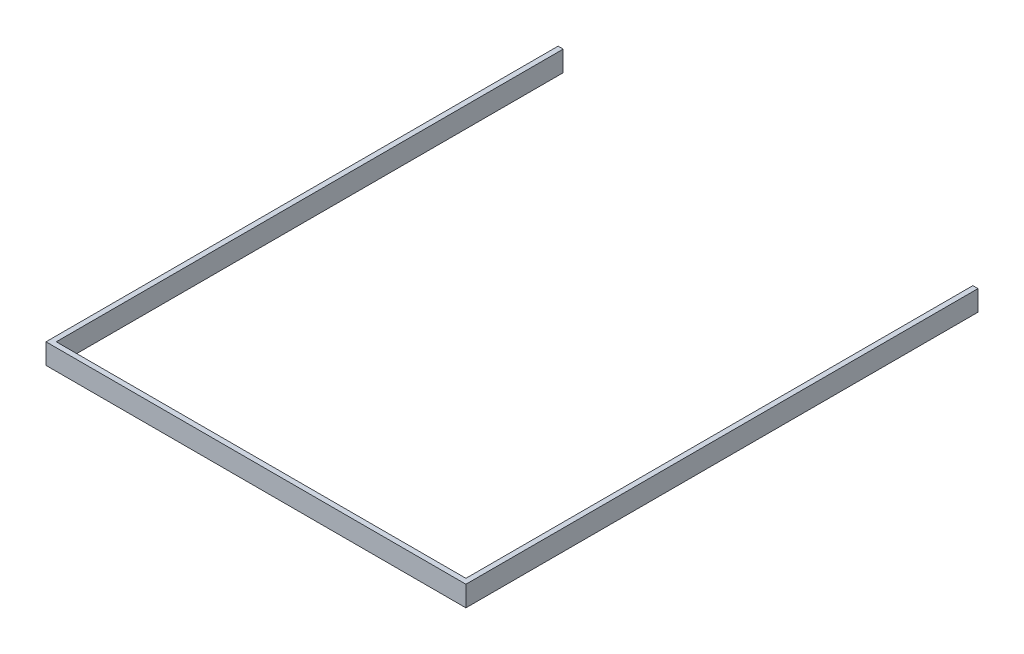
SolidWorks part; units mm, degrees
ref_plane "Plan de face" through (0, 0, 0) normal (0, 0, 1) x (1, 0, 0)
ref_plane "Plan de dessus" through (0, 0, 0) normal (0, 1, 0) x (1, 0, 0)
ref_plane "Plan de droite" through (0, 0, 0) normal (1, 0, 0) x (0, 0, -1)
sketch "Esquisse1" plane through (0, 0, 0) normal (0, 0, 1) x (1, 0, 0)
  line L1 (0, 0) -> (164, 0)
  line L2 (0, 0) -> (0, -8)
  line L3 (0, -8) -> (164, -8)
  line L4 (164, 0) -> (164, -8)
  dimension "D1" = 164
  dimension "D2" = 8
extrude "Boss.-Extru.1" add sketch "Esquisse1" along normal blind 200
sketch "Esquisse2" plane through (0, 0, 0) normal (0, 0, 1) x (1, 0, 0)
  line L0 (164, 0) -> (0, 0) construction
  line L1 (2, 0) -> (162, 0)
  line L2 (2, 0) -> (2, -8)
  line L3 (2, -8) -> (162, -8)
  line L4 (162, 0) -> (162, -8)
  line L5 (0, -8) -> (164, -8) construction
  line L6 (0, 0) -> (0, -8) construction
  line L7 (164, -8) -> (164, 0) construction
  point P10 (0, -4)
  point P11 (162, -4)
  dimension "D1" = 2
  dimension "D2" = 2
extrude "Enlèv. mat.-Extru.2" cut sketch "Esquisse2" along normal blind 198
